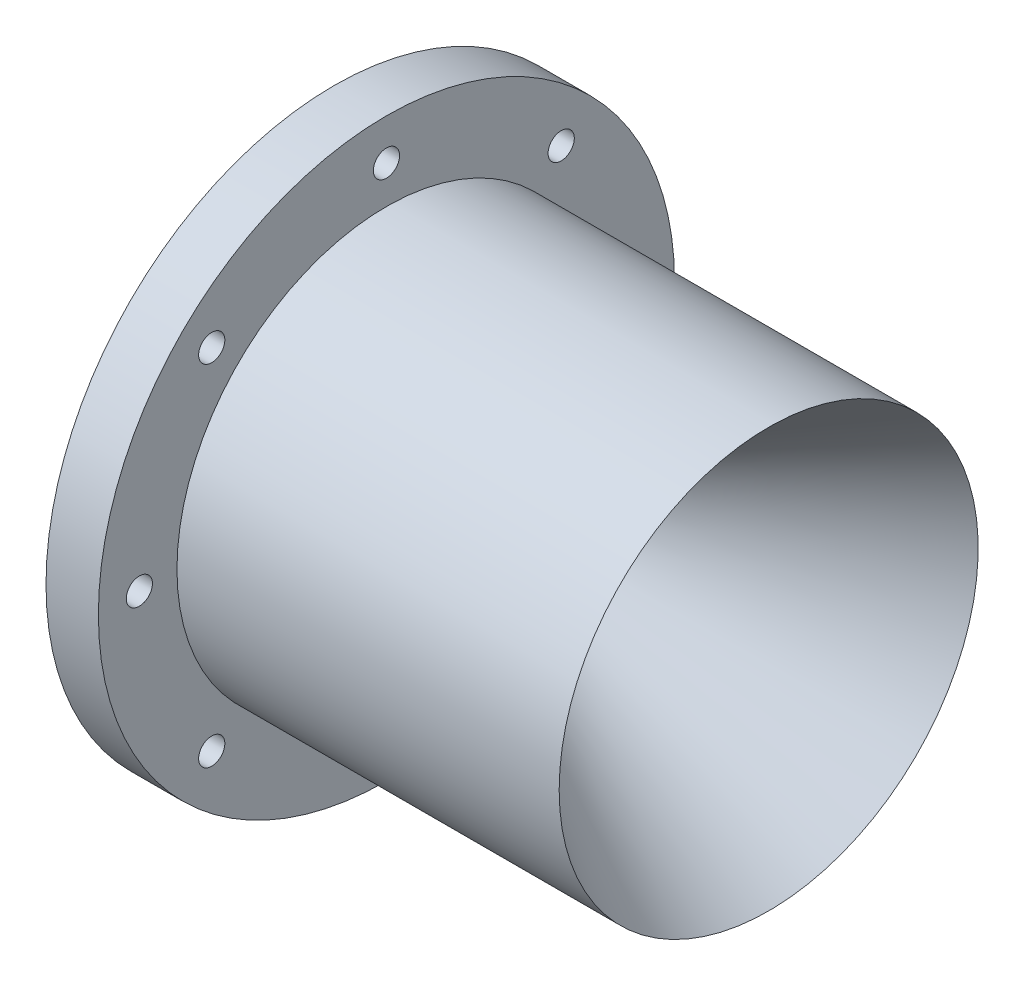
SolidWorks part; units mm, degrees
material "C (Graphite)"
ref_plane "Front Plane" through (0, 0, 0) normal (0, 0, 1) x (1, 0, 0)
ref_plane "Top Plane" through (0, 0, 0) normal (0, 1, 0) x (1, 0, 0)
ref_plane "Right Plane" through (0, 0, 0) normal (1, 0, 0) x (0, 0, -1)
sketch "Sketch1" plane through (0, 0, 0) normal (0, 0, 1) x (1, 0, 0)
  line L0 (0, 0) -> (215.3765, 0) construction
  line L1 (0, 0) -> (0, 93.6004) construction
  line L3 (0, 7.9375) -> (72.3242, 50.8)
  line L10 (0, 7.9375) -> (-12.7, 7.9375)
  line L22 (-12.7, 7.9375) -> (-33.0473, 41.275)
  line L23 (-33.0473, 50.8) -> (-33.0473, 41.275)
  line L24 (-33.0473, 50.8) -> (-33.0473, 69.85)
  line L25 (-33.0473, 69.85) -> (-20.3473, 69.85)
  line L26 (-20.3473, 69.85) -> (-20.3473, 50.8)
  line L27 (-20.3473, 50.8) -> (72.3242, 50.8)
  dimension "D3" = 7.9375
  dimension "D4" = 9.525
  dimension "D7" = 12.7
  dimension "D10" = 50.8
  dimension "D11" = 19.05
  dimension "D12" = 12.7
revolve "Revolve1" add sketch "Sketch1" angle 360 about L0
sketch "Sketch3" plane through (-33.0473, 0, 0) normal (-1, 0, 0) x (0, 0, 1)
  circle A0 centre (0, 59.9186) radius 3.175
  circle A1 centre (42.3688, 42.3688) radius 3.175
  circle A2 centre (59.9186, 0) radius 3.175
  circle A3 centre (42.3688, -42.3688) radius 3.175
  circle A4 centre (0, -59.9186) radius 3.175
  circle A5 centre (-42.3688, -42.3688) radius 3.175
  circle A6 centre (-59.9186, 0) radius 3.175
  circle A7 centre (-42.3688, 42.3688) radius 3.175
  point P36 (0, 0)
  dimension "D1" = 6.35
  dimension "D2" = 59.9186
  dimension "D3" = 8
extrude "Cut-Extrude2" cut sketch "Sketch3" against normal up to next
